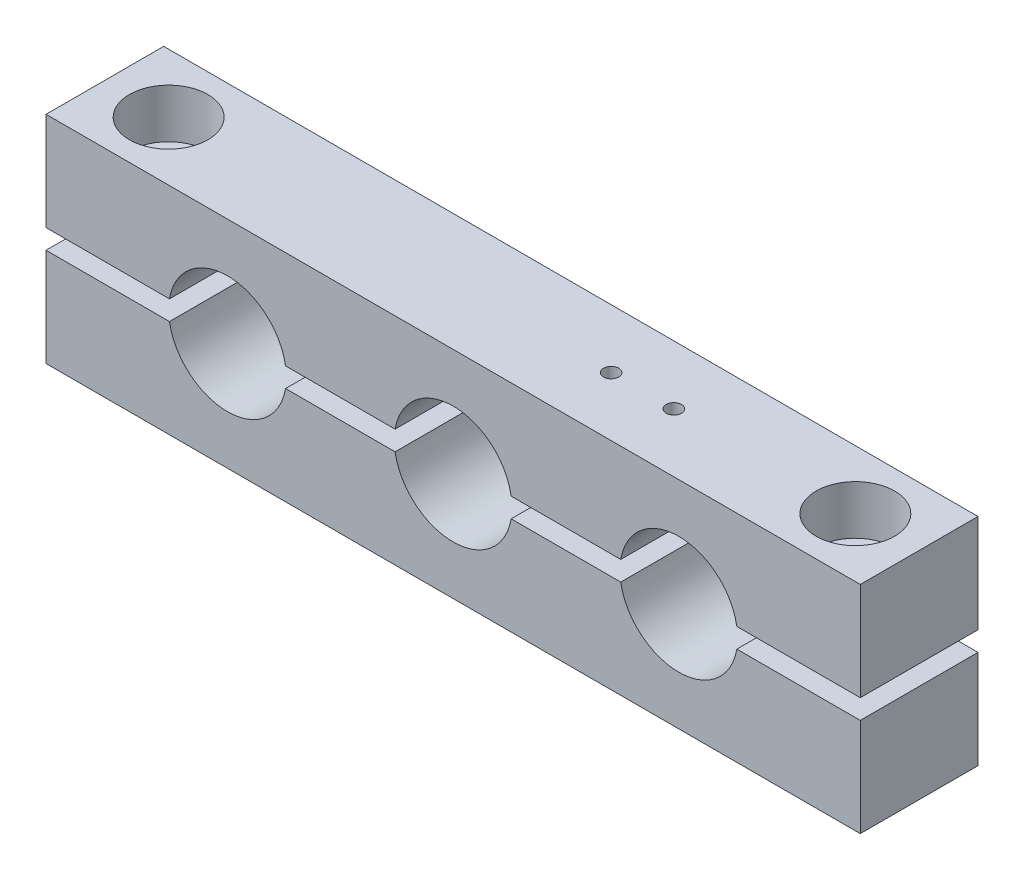
SolidWorks part; units mm, degrees
ref_plane "Front Plane" through (0, 0, 0) normal (0, 0, 1) x (1, 0, 0)
ref_plane "Top Plane" through (0, 0, 0) normal (0, 1, 0) x (1, 0, 0)
ref_plane "Right Plane" through (0, 0, 0) normal (1, 0, 0) x (0, 0, -1)
sketch "Sketch1" plane through (0, 0, 0) normal (0, 0, 1) x (1, 0, 0)
  line L0 (0, 23.65) -> (0, -22.65) construction
  line L1 (-41.5, -11) -> (41.5, -11)
  line L2 (-41.5, -11) -> (-41.5, 11)
  line L3 (-41.5, 11) -> (41.5, 11)
  line L4 (41.5, -11) -> (41.5, 11)
  line L5 (-41.5, -11) -> (41.5, 11) construction
  line L6 (-41.5, 11) -> (41.5, -11) construction
  circle A0 centre (0, 0) radius 6
  circle A1 centre (-23, 0) radius 6
  circle A2 centre (23, 0) radius 6
  point P0 (0, 0)
  dimension "D1" = 12
  dimension "D2" = 23
  dimension "D3" = 83
  dimension "D4" = 22
extrude "Boss-Extrude1" add sketch "Sketch1" along normal blind 12
sketch "Sketch2" plane through (0, 11, 0) normal (0, 1, 0) x (1, 0, 0)
  line L0 (0, 9.7473) -> (0, -23.225) construction
  line L1 (-47.7498, -6) -> (47.8421, -6) construction
  line L2 (41.5, 0) -> (-41.5, 0) construction
  circle A0 centre (-35, -6) radius 2.1
  circle A1 centre (35, -6) radius 2.1
  dimension "D2" = 4.2
  dimension "D1" = 6
  dimension "D3" = 35
extrude "Cut-Extrude1" cut sketch "Sketch2" against normal through all
sketch "Sketch3" plane through (0, 11, 0) normal (0, 1, 0) x (1, 0, 0)
  circle A0 centre (-35, -6) radius 4
  circle A1 centre (35, -6) radius 4
  dimension "D1" = 8
  dimension "D2" = 35
extrude "Cut-Extrude2" cut sketch "Sketch3" against normal blind 5
sketch "Sketch4" plane through (0, 0, 12) normal (0, 0, 1) x (1, 0, 0)
  line L1 (-48.1192, 1) -> (48.1192, 1)
  line L2 (-48.1192, 1) -> (-48.1192, -1)
  line L3 (-48.1192, -1) -> (48.1192, -1)
  line L4 (48.1192, 1) -> (48.1192, -1)
  line L5 (-48.1192, 1) -> (48.1192, -1) construction
  line L6 (-48.1192, -1) -> (48.1192, 1) construction
  point P0 (0, 0)
  dimension "D1" = 2
extrude "Cut-Extrude3" cut sketch "Sketch4" against normal through all
sketch "Sketch5" plane through (0, 11, 0) normal (0, 1, 0) x (1, 0, 0)
  line L0 (41.5, -6) -> (-44.6698, -6) construction
  line L1 (41.5, -12) -> (41.5, 0) construction
  circle A0 centre (16.5, -6) radius 0.78
  circle A1 centre (10.1, -6) radius 0.78
  dimension "D1" = 6.4
  dimension "D3" = 1.56
  dimension "D2" = 25
extrude "Cut-Extrude4" cut sketch "Sketch5" against normal blind 8
